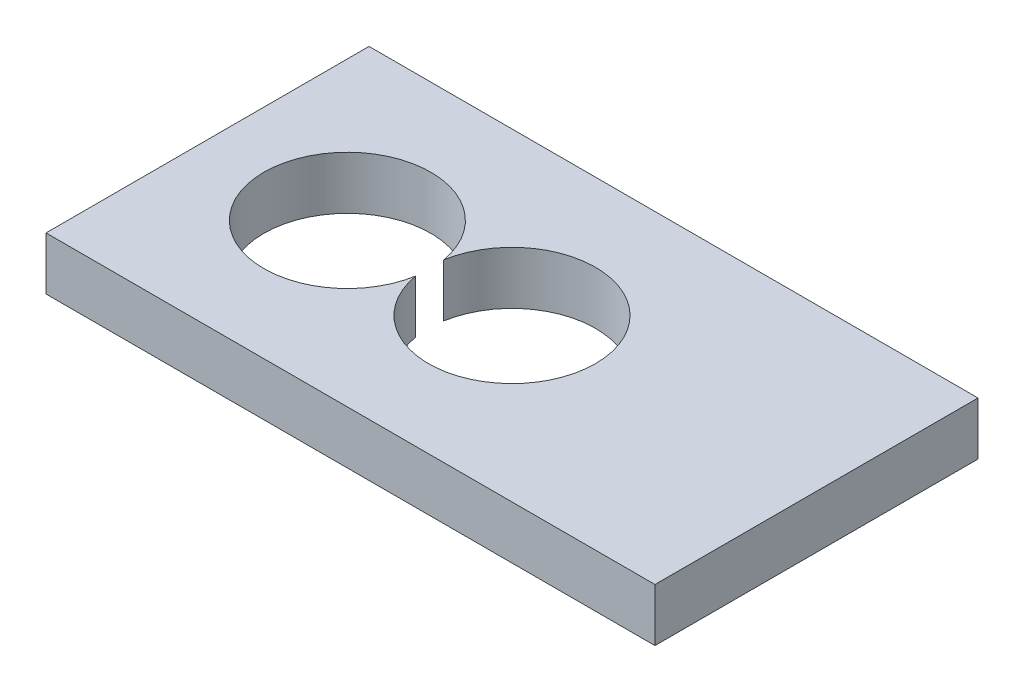
SolidWorks part; units mm, degrees
ref_plane "Front Plane" through (0, 0, 0) normal (0, 0, 1) x (1, 0, 0)
ref_plane "Top Plane" through (0, 0, 0) normal (0, 1, 0) x (1, 0, 0)
ref_plane "Right Plane" through (0, 0, 0) normal (1, 0, 0) x (0, 0, -1)
sketch "Sketch1" plane through (0, 0, 0) normal (0, 1, 0) x (1, 0, 0)
  line L1 (-25.8927, 13.7352) -> (25.8927, 13.7352)
  line L2 (-25.8927, 13.7352) -> (-25.8927, -13.7352)
  line L3 (-25.8927, -13.7352) -> (25.8927, -13.7352)
  line L4 (25.8927, 13.7352) -> (25.8927, -13.7352)
  line L5 (-25.8927, 13.7352) -> (25.8927, -13.7352) construction
  line L6 (-25.8927, -13.7352) -> (25.8927, 13.7352) construction
  circle A0 centre (0, 0) radius 6 construction
  circle A1 centre (-14, 0) radius 8 construction
  arc A2 (-7, 1.1874) -> (-7, -1.1874) centre (-14, 0) ccw
  arc A3 (-7, -1.1874) -> (-7, 1.1874) centre (0, 0) ccw
  dimension "D1" = 12
  dimension "D2" = 16
  dimension "D3" = 14.2
  dimension "D4" = 14.2
extrude "Boss-Extrude1" add sketch "Sketch1" against normal blind 4.5
equation "\"drive_gear_tooth_count\"= 20"
equation "\"driven_gear_tooth_count\"= 15"
equation "\"drive_gear_pitch_diameter\"= \"drive_gear_tooth_count\" * 0.8mm"
equation "\"driven_gear_pitch_diameter\"= \"driven_gear_tooth_count\" * 0.8mm"
equation "\"D1@Sketch1\"=\"driven_gear_pitch_diameter\""
equation "\"D2@Sketch1\"=\"drive_gear_pitch_diameter\""
